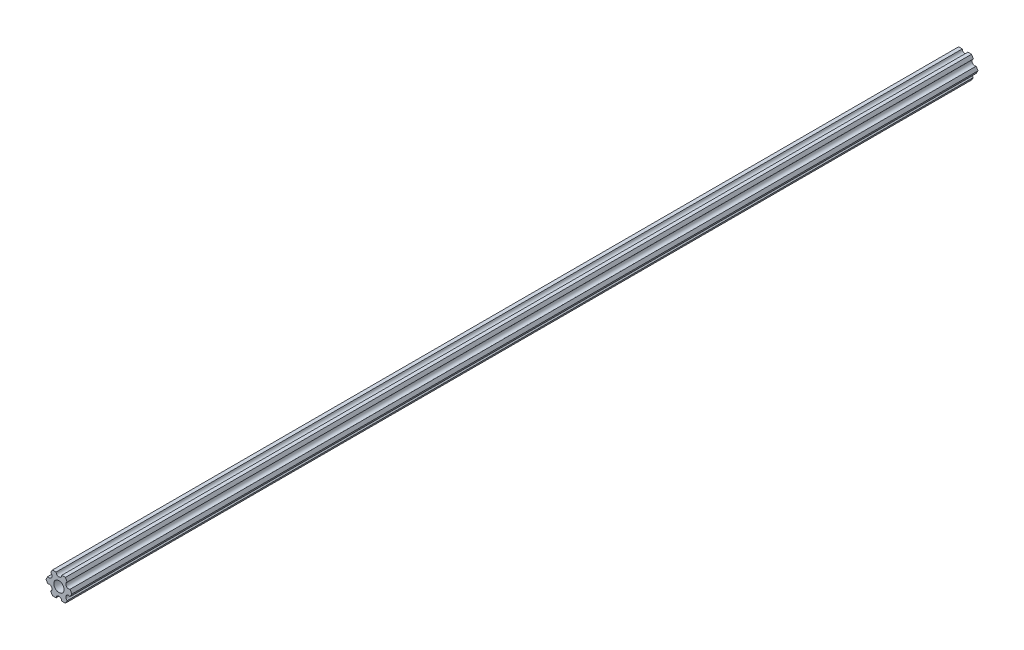
SolidWorks part; units mm, degrees
ref_plane "Front Plane" through (0, 0, 0) normal (0, 0, 1) x (1, 0, 0)
ref_plane "Top Plane" through (0, 0, 0) normal (0, 1, 0) x (1, 0, 0)
ref_plane "Right Plane" through (0, 0, 0) normal (1, 0, 0) x (0, 0, -1)
sketch "Sketch1" plane through (0, 0, 0) normal (0, 0, 1) x (1, 0, 0)
  line L0 (-1.5875, 6.35) -> (-3.6662, 6.35)
  line L1 (7.3323, 0) -> (6.293, 1.8002)
  line L2 (3.6662, 6.35) -> (1.5875, 6.35)
  line L3 (-3.6662, 6.35) -> (-4.7055, 4.5498)
  line L4 (-7.3323, 0) -> (-6.293, -1.8002)
  line L5 (-3.6662, -6.35) -> (-1.5875, -6.35)
  line L6 (3.6662, -6.35) -> (4.7055, -4.5498)
  line L7 (-6.293, 1.8002) -> (-7.3323, 0)
  line L8 (-4.7055, -4.5498) -> (-3.6662, -6.35)
  line L9 (1.5875, -6.35) -> (3.6662, -6.35)
  line L10 (6.293, -1.8002) -> (7.3323, 0)
  line L11 (4.7055, 4.5498) -> (3.6662, 6.35)
  circle A0 centre (0, 0) radius 2.9337
  arc A2 (-1.5875, 6.35) -> (1.5875, 6.35) centre (0, 6.35) ccw
  arc A3 (4.7055, 4.5498) -> (6.293, 1.8002) centre (5.4993, 3.175) ccw
  arc A4 (6.293, -1.8002) -> (4.7055, -4.5498) centre (5.4993, -3.175) ccw
  arc A5 (1.5875, -6.35) -> (-1.5875, -6.35) centre (0, -6.35) ccw
  arc A6 (-4.7055, -4.5498) -> (-6.293, -1.8002) centre (-5.4993, -3.175) ccw
  arc A7 (-6.293, 1.8002) -> (-4.7055, 4.5498) centre (-5.4993, 3.175) ccw
  dimension "D1" = 5.8674
  dimension "D3" = 3.175
  dimension "D4" = 6
extrude "Boss-Extrude1" add sketch "Sketch1" along normal blind 514.35
